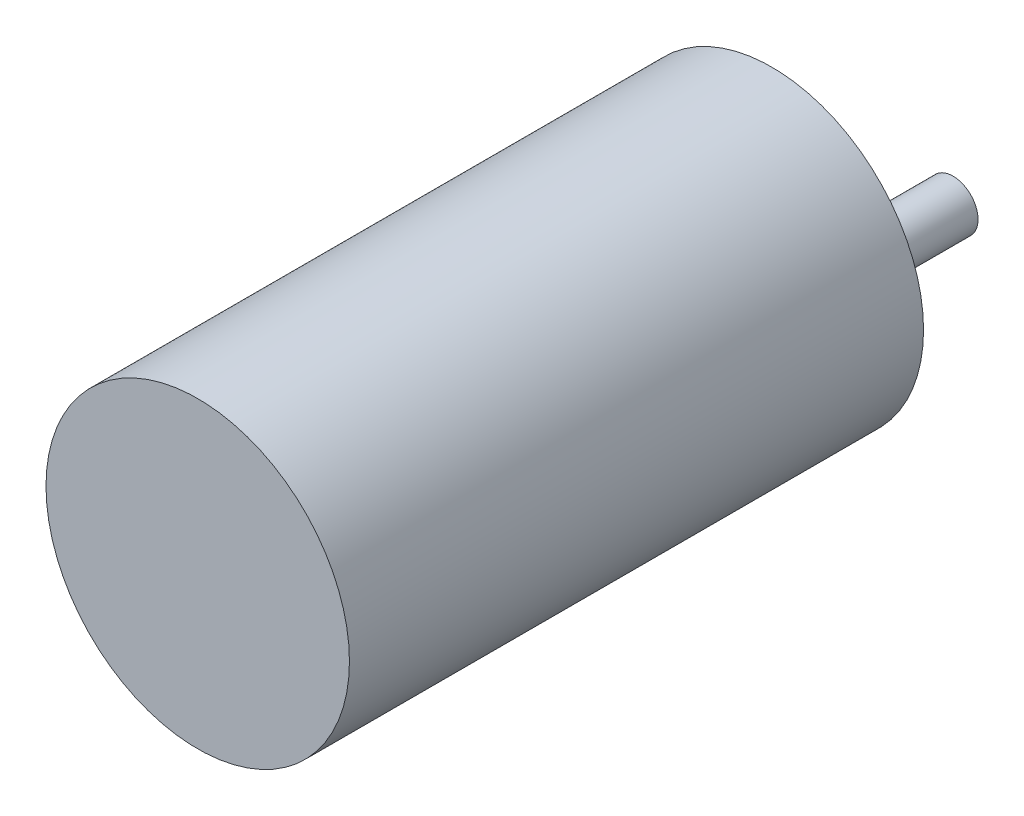
SolidWorks part; units mm, degrees
ref_plane "Front Plane" through (0, 0, 0) normal (0, 0, 1) x (1, 0, 0)
ref_plane "Top Plane" through (0, 0, 0) normal (0, 1, 0) x (1, 0, 0)
ref_plane "Right Plane" through (0, 0, 0) normal (1, 0, 0) x (0, 0, -1)
sketch "Sketch1" plane through (0, 0, 0) normal (0, 0, 1) x (1, 0, 0)
  circle A0 centre (0, 0) radius 18.5
  dimension "D1" = 37
extrude "Boss-Extrude1" add sketch "Sketch1" along normal blind 70
sketch "Sketch2" plane through (0, 0, 0) normal (0, 0, -1) x (-1, 0, 0)
  circle A0 centre (0, -7.112) radius 5.969
  point P2 (0, 0)
  dimension "D2" = 11.938
  dimension "D1" = 7.112
extrude "Boss-Extrude2" add sketch "Sketch2" along normal blind 6.096
sketch "Sketch3" plane through (0, 0, -6.096) normal (0, 0, -1) x (-1, 0, 0)
  circle A0 centre (0, -7.112) radius 3.048
  dimension "D1" = 6.096
extrude "Boss-Extrude3" add sketch "Sketch3" along normal blind 16.002
sketch "Sketch4" plane through (0, 0, 0) normal (0, 0, -1) x (-1, 0, 0)
  line L6 (-15.2766, 0) -> (-7.7942, 13.2141) construction
  line L7 (7.7942, 13.2141) -> (15.2766, 0) construction
  line L8 (-15.2766, 0) -> (15.2766, 0) construction
  line L9 (-15.2766, 0) -> (-7.7942, -13.5675) construction
  line L10 (7.7942, -13.5675) -> (15.2766, 0) construction
  line L11 (-16.8766, 0) -> (-18.5, 0) construction
  line L12 (-7.7942, 13.2141) -> (-8.9086, 16.2138) construction
  circle A0 centre (-15.2766, 0) radius 1.6
  circle A1 centre (15.2766, 0) radius 1.6
  circle A2 centre (7.7942, -13.5675) radius 1.6
  circle A3 centre (-7.7942, -13.5675) radius 1.6
  circle A4 centre (-7.7942, 13.2141) radius 1.6
  circle A5 centre (7.7942, 13.2141) radius 1.6
  circle A7 centre (0, 0) radius 18.5 construction
  point P12 (0, 0)
  point P18 (-8.3514, 14.714)
  dimension "D1" = 1.6234
  dimension "D4" = 3.2
  dimension "D2" = 30.988
  dimension "D3" = 15.494
  dimension "D5" = 2.9997
extrude "Cut-Extrude1" cut sketch "Sketch4" against normal blind 3
